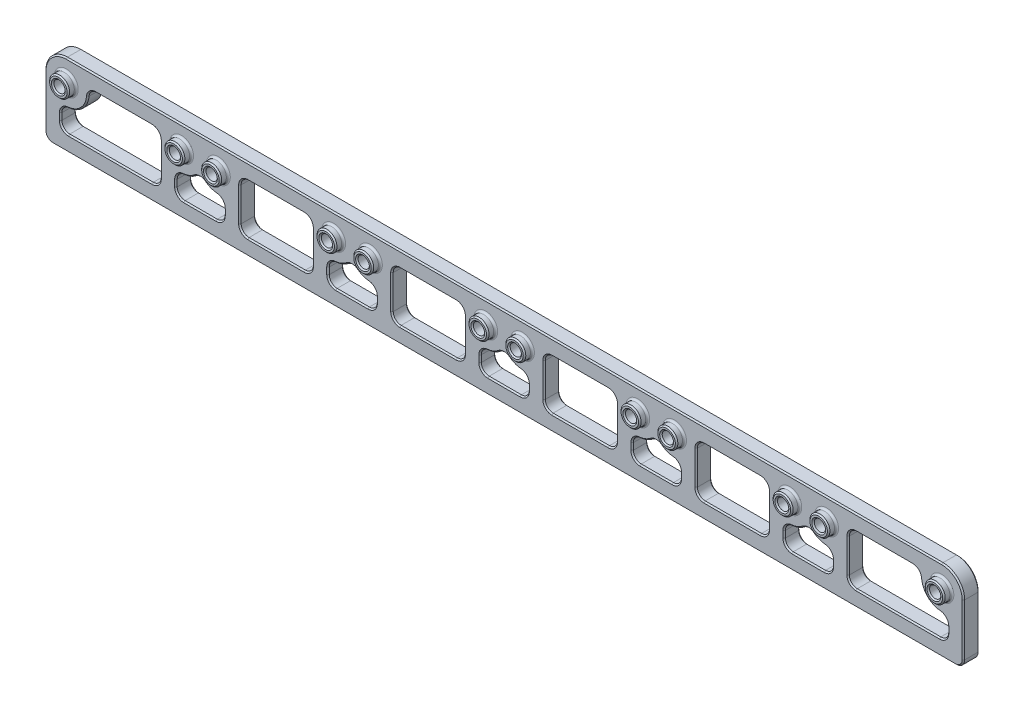
SolidWorks part; units mm, degrees
ref_plane "Front Plane" through (0, 0, 0) normal (0, 0, 1) x (1, 0, 0)
ref_plane "Top Plane" through (0, 0, 0) normal (0, 1, 0) x (1, 0, 0)
ref_plane "Right Plane" through (0, 0, 0) normal (1, 0, 0) x (0, 0, -1)
sketch "Sketch1" plane through (0, 0, 0) normal (0, 0, 1) x (1, 0, 0)
  line L0 (92.075, 4.3205) -> (92.075, -11.999)
  line L1 (92.075, -11.999) -> (-92.075, -11.999)
  line L2 (-92.075, -11.999) -> (-92.075, 4.3205)
  line L18 (92.075, 0) -> (-92.075, 0) construction
  line L19 (92.075, 4.3205) -> (-92.075, 4.3205)
  point P0 (88.5448, 5.9995)
  dimension "D1" = 4.3205
  dimension "D2" = 184.15
  dimension "D3" = 11.999
extrude "Boss-Extrude1" add sketch "Sketch1" along normal mid plane 3.175
sketch "Sketch2" plane through (0, 0, 1.5875) normal (0, 0, 1) x (1, 0, 0)
  line L0 (-3.6855, 0) -> (3.6855, 0) construction
  line L1 (-87.7545, 0) -> (-64.6455, 0) construction
  line L2 (-64.6455, 0) -> (-57.2745, 0) construction
  line L3 (-57.2745, 0) -> (-34.1655, 0) construction
  line L4 (-34.1655, 0) -> (-26.7945, 0) construction
  line L5 (-26.7945, 0) -> (-3.6855, 0) construction
  line L6 (3.6855, 0) -> (26.7945, 0) construction
  line L7 (26.7945, 0) -> (34.1655, 0) construction
  line L8 (34.1655, 0) -> (57.2745, 0) construction
  line L9 (57.2745, 0) -> (64.6455, 0) construction
  line L10 (64.6455, 0) -> (87.7545, 0) construction
  circle A0 centre (-87.7545, 0) radius 2.0002
  circle A1 centre (-64.6455, 0) radius 2.0002
  circle A2 centre (-57.2745, 0) radius 2.0003
  circle A3 centre (-34.1655, 0) radius 2.0003
  circle A4 centre (-26.7945, 0) radius 2.0003
  circle A5 centre (-3.6855, 0) radius 2.0002
  circle A6 centre (3.6855, 0) radius 2.0003
  circle A7 centre (26.7945, 0) radius 2.0002
  circle A8 centre (34.1655, 0) radius 2.0003
  circle A9 centre (57.2745, 0) radius 2.0003
  circle A10 centre (64.6455, 0) radius 2.0002
  circle A11 centre (87.7545, 0) radius 2.0002
  dimension "D1" = 4.0005
  dimension "D2" = 23.1089
  dimension "D3" = 7.3711
  dimension "D4" = 23.1089
  dimension "D5" = 7.3711
  dimension "D6" = 23.1089
  dimension "D7" = 7.3711
  dimension "D8" = 23.1089
  dimension "D9" = 7.3711
  dimension "D10" = 23.1089
  dimension "D11" = 7.3711
  dimension "D12" = 23.1089
extrude "Boss-Extrude2" add sketch "Sketch2" along normal blind 1.5875 contours A0
hole_wizard "#4-40 Tapped Hole1" positions "Sketch3" profile "Sketch4" tap size "#4-40" standard "ANSI Inch" end condition through all
sketch "Sketch3" plane through (0, 0, 3.175) normal (0, 0, 1) x (1, 0, 0)
  circle A0 centre (-87.7545, 0) radius 2.0002 construction
  point P0 (-87.7545, 0)
  point P2 (-64.6455, 0)
  point P5 (-57.2745, 0)
  point P8 (-34.1655, 0)
  point P11 (-26.7945, 0)
  point P14 (-3.6855, 0)
  point P17 (3.6855, 0)
  point P20 (26.7945, 0)
  point P23 (34.1655, 0)
  point P26 (57.2745, 0)
  point P29 (64.6455, 0)
  point P32 (87.7545, 0)
sketch "Sketch4" plane through (-87.7545, 0, 3.175) normal (1, 0, 0) x (0, -1, 0)
  line L0 (0, 0) -> (0, 4.7625)
  line L1 (0, 4.7625) -> (1.1303, 4.7625)
  line L2 (1.1303, 4.7625) -> (1.1303, 0)
  line L5 (1.1303, 0) -> (0, 0)
  line L11 (0, -6.35) -> (0, 107.95) construction
  dimension "Thru Tap Drill Dia." = 2.2606
  dimension "Thru Tap Drill Depth" = 4.7625
cosmetic thread "Hole Thread1" parameters "D2"=2.8448
cosmetic thread "Hole Thread2" parameters "D2"=2.8448
cosmetic thread "Hole Thread3" parameters "D2"=2.8448
cosmetic thread "Hole Thread4" parameters "D2"=2.8448
cosmetic thread "Hole Thread5" parameters "D2"=2.8448
cosmetic thread "Hole Thread6" parameters "D2"=2.8448
cosmetic thread "Hole Thread7" parameters "D2"=2.8448
cosmetic thread "Hole Thread8" parameters "D2"=2.8448
cosmetic thread "Hole Thread9" parameters "D2"=2.8448
cosmetic thread "Hole Thread10" parameters "D2"=2.8448
cosmetic thread "Hole Thread11" parameters "D2"=2.8448
cosmetic thread "Hole Thread12" parameters "D2"=2.8448
sketch "Sketch5" plane through (0, 0, 1.5875) normal (0, 0, 1) x (1, 0, 0)
  line L0 (92.075, 4.3205) -> (-92.075, 4.3205) construction
  line L1 (-83.5844, 1.1303) -> (-68.8156, 1.1303)
  line L2 (-53.1044, 1.1303) -> (-38.3356, 1.1303)
  line L3 (-22.6244, 1.1303) -> (-7.8556, 1.1303)
  line L4 (7.8556, 1.1303) -> (22.6244, 1.1303)
  line L5 (38.3356, 1.1303) -> (53.1044, 1.1303)
  line L6 (68.8156, 1.1303) -> (83.5844, 1.1303)
  line L7 (-88.8848, -4.1701) -> (-88.8848, -8.8087)
  line L8 (-92.075, 4.3205) -> (-92.075, -11.999) construction
  line L9 (-88.8848, -8.8087) -> (-68.9661, -8.8087)
  line L10 (-68.9661, -8.8087) -> (-68.9661, 0)
  line L11 (-92.075, -11.999) -> (92.075, -11.999) construction
  line L12 (-65.7758, -4.1701) -> (-65.7758, -8.8087)
  line L13 (-65.7758, -8.8087) -> (-56.1442, -8.8087)
  line L14 (-56.1442, -8.8087) -> (-56.1442, -4.1701)
  line L15 (-52.9539, 0) -> (-52.9539, -8.8087)
  line L16 (-52.9539, -8.8087) -> (-38.4861, -8.8087)
  line L17 (-38.4861, -8.8087) -> (-38.4861, 0)
  line L18 (-35.2958, -4.1701) -> (-35.2958, -8.8087)
  line L19 (-35.2958, -8.8087) -> (-25.6642, -8.8087)
  line L20 (-25.6642, -8.8087) -> (-25.6642, -4.1701)
  line L21 (-22.4739, 0) -> (-22.4739, -8.8087)
  line L22 (-22.4739, -8.8087) -> (-8.0061, -8.8087)
  line L23 (-8.0061, -8.8087) -> (-8.0061, 0)
  line L24 (-4.8158, -4.1701) -> (-4.8158, -8.8087)
  line L25 (-4.8158, -8.8087) -> (4.8158, -8.8087)
  line L26 (4.8158, -8.8087) -> (4.8158, -4.1701)
  line L27 (8.0061, 0) -> (8.0061, -8.8087)
  line L28 (8.0061, -8.8087) -> (22.4739, -8.8087)
  line L29 (22.4739, -8.8087) -> (22.4739, 0)
  line L30 (25.6642, -4.1701) -> (25.6642, -8.8087)
  line L31 (25.6642, -8.8087) -> (35.2958, -8.8087)
  line L32 (35.2958, -8.8087) -> (35.2958, -4.1701)
  line L33 (38.4861, 0) -> (38.4861, -8.8087)
  line L34 (38.4861, -8.8087) -> (52.9539, -8.8087)
  line L35 (52.9539, -8.8087) -> (52.9539, 0)
  line L36 (56.1442, -4.1701) -> (56.1442, -8.8087)
  line L37 (56.1442, -8.8087) -> (65.7758, -8.8087)
  line L38 (65.7758, -8.8087) -> (65.7758, -4.1701)
  line L39 (68.9661, 0) -> (68.9661, -8.8087)
  line L40 (68.9661, -8.8087) -> (88.8848, -8.8087)
  line L41 (88.8848, -4.1701) -> (88.8848, -8.8087)
  line L42 (92.075, -11.999) -> (92.075, 4.3205) construction
  line L43 (-92.075, 0) -> (-92.075, 4.3205)
  line L44 (-92.075, 4.3205) -> (-87.7545, 4.3205)
  line L45 (87.7545, 4.3205) -> (92.075, 4.3205)
  line L46 (92.075, 4.3205) -> (92.075, 0)
  arc A0 (-88.8848, -4.1701) -> (-83.5844, 1.1303) centre (-87.7545, 0) ccw
  arc A1 (-68.8156, 1.1303) -> (-68.9661, 0) centre (-64.6455, 0) ccw
  arc A2 (-60.96, -2.2547) -> (-56.1442, -4.1701) centre (-57.2745, 0) ccw
  arc A3 (-38.3356, 1.1303) -> (-38.4861, 0) centre (-34.1655, 0) ccw
  arc A4 (-30.48, -2.2547) -> (-25.6642, -4.1701) centre (-26.7945, 0) ccw
  arc A5 (-7.8556, 1.1303) -> (-8.0061, 0) centre (-3.6855, 0) ccw
  arc A6 (0, -2.2547) -> (4.8158, -4.1701) centre (3.6855, 0) ccw
  arc A7 (22.6244, 1.1303) -> (22.4739, 0) centre (26.7945, 0) ccw
  arc A8 (30.48, -2.2547) -> (35.2958, -4.1701) centre (34.1655, 0) ccw
  arc A9 (53.1044, 1.1303) -> (52.9539, 0) centre (57.2745, 0) ccw
  arc A10 (60.96, -2.2547) -> (65.7758, -4.1701) centre (64.6455, 0) ccw
  arc A11 (83.5844, 1.1303) -> (88.8848, -4.1701) centre (87.7545, 0) ccw
  arc A12 (-65.7758, -4.1701) -> (-60.96, -2.2547) centre (-64.6455, 0) ccw
  arc A13 (-52.9539, 0) -> (-53.1044, 1.1303) centre (-57.2745, 0) ccw
  arc A14 (-35.2958, -4.1701) -> (-30.48, -2.2547) centre (-34.1655, 0) ccw
  arc A15 (-22.4739, 0) -> (-22.6244, 1.1303) centre (-26.7945, 0) ccw
  arc A16 (-4.8158, -4.1701) -> (0, -2.2547) centre (-3.6855, 0) ccw
  arc A17 (8.0061, 0) -> (7.8556, 1.1303) centre (3.6855, 0) ccw
  arc A18 (25.6642, -4.1701) -> (30.48, -2.2547) centre (26.7945, 0) ccw
  arc A19 (38.4861, 0) -> (38.3356, 1.1303) centre (34.1655, 0) ccw
  arc A20 (68.9661, 0) -> (68.8156, 1.1303) centre (64.6455, 0) ccw
  arc A21 (56.1442, -4.1701) -> (60.96, -2.2547) centre (57.2745, 0) ccw
  arc A22 (-87.7545, 4.3205) -> (-92.075, 0) centre (-87.7545, 0) ccw
  arc A23 (92.075, 0) -> (87.7545, 4.3205) centre (87.7545, 0) ccw
  point P66 (-56.1442, -6.4894)
  dimension "D1" = 3.1902
  dimension "D2" = 3.1902
  dimension "D3" = 3.1902
  dimension "D4" = 3.1902
  dimension "D5" = 3.1902
  dimension "D6" = 3.1902
  dimension "D7" = 3.1902
  dimension "D8" = 3.1902
  dimension "D9" = 3.1902
  dimension "D10" = 3.1902
  dimension "D11" = 3.1902
  dimension "D12" = 3.1902
  dimension "D13" = 3.1902
  dimension "D14" = 3.1902
extrude "Cut-Extrude1" cut sketch "Sketch5" against normal through all both and the other way through all contours A4 L20 L19 L18 A14
fillet "Fillet1" radius 0.3969 12 edges at (85.7542, 0, 1.5875) (62.6453, 0, 1.5875) (55.2742, 0, 1.5875) (32.1653, 0, 1.5875) (24.7942, 0, 1.5875) (1.6853, 0, 1.5875) (-5.6858, 0, 1.5875) (-28.7947, 0, 1.5875) (-36.1658, 0, 1.5875) (-59.2747, 0, 1.5875) (-66.6458, 0, 1.5875) (-89.7547, 0, 1.5875)
fillet "Fillet2" radius 1.5875 53 edges at (-92.075, -11.999, 0) (92.075, -11.999, 0) (83.5844, 1.1303, 0) (88.8848, -4.1701, 0) (88.8848, -8.8087, 0) (68.9661, -8.8087, 0) (68.8156, 1.1303, 0) (65.7758, -4.1701, 0) (65.7758, -8.8087, 0) (56.1442, -8.8087, 0) (56.1442, -4.1701, 0) (60.96, -2.2547, 0) (53.1044, 1.1303, 0) (52.9539, -8.8087, 0) (38.4861, -8.8087, 0) (38.3356, 1.1303, 0) (25.6642, -4.1701, 0) (30.48, -2.2547, 0) (35.2958, -4.1701, 0) (35.2958, -8.8087, 0) (25.6642, -8.8087, 0) (8.0061, -8.8087, 0) (22.4739, -8.8087, 0) (22.6244, 1.1303, 0) (7.8556, 1.1303, 0) (-4.8158, -4.1701, 0) (4.8158, -4.1701, 0) (0, -2.2547, 0) (-4.8158, -8.8087, 0) (4.8158, -8.8087, 0) (-8.0061, -8.8087, 0) (-7.8556, 1.1303, 0) (-22.6244, 1.1303, 0) (-22.4739, -8.8087, 0) (-25.6642, -8.8087, 0) (-25.6642, -4.1701, 0) (-30.48, -2.2547, 0) (-35.2958, -4.1701, 0) (-35.2958, -8.8087, 0) (-38.4861, -8.8087, 0) (-38.3356, 1.1303, 0) (-53.1044, 1.1303, 0) (-52.9539, -8.8087, 0) (-56.1442, -8.8087, 0) (-65.7758, -8.8087, 0) (-65.7758, -4.1701, 0) (-56.1442, -4.1701, 0) (-88.8848, -4.1701, 0) (-88.8848, -8.8087, 0) (-68.9661, -8.8087, 0) (-68.8156, 1.1303, 0) (-83.5844, 1.1303, 0) (-60.96, -2.2547, 0)
chamfer "Chamfer2" distance 0.254 angle 45 256 edges at (89.7547, 0, 3.175) (66.6458, 0, 3.175) (59.2747, 0, 3.175) (36.1658, 0, 3.175) (28.7947, 0, 3.175) (5.6858, 0, 3.175) (-1.6853, 0, 3.175) (-24.7942, 0, 3.175) (-32.1653, 0, 3.175) (-55.2742, 0, 3.175) (-62.6453, 0, 3.175) (-85.7542, 0, 3.175) (88.8848, 0, 3.175) (88.8848, 0, -1.5875) (65.7758, 0, 3.175) (65.7758, 0, -1.5875) (58.4048, 0, 3.175) (58.4048, 0, -1.5875) (35.2958, 0, 3.175) (35.2958, 0, -1.5875) (27.9248, 0, 3.175) (27.9248, 0, -1.5875) (4.8158, 0, 3.175) (4.8158, 0, -1.5875) (-2.5552, 0, 3.175) (-2.5552, 0, -1.5875) (-25.6642, 0, 3.175) (-25.6642, 0, -1.5875) (-33.0352, 0, 3.175) (-33.0352, 0, -1.5875) (-56.1442, 0, 3.175) (-56.1442, 0, -1.5875) (-63.5152, 0, 3.175) (-63.5152, 0, -1.5875) (-86.6242, 0, 3.175) (-86.6242, 0, -1.5875) (82.9424, 0.708, -1.5875) (84.6994, -3.0551, -1.5875) (88.4624, -4.8121, -1.5875) (88.8848, -6.5558, -1.5875) (88.4198, -8.3438, -1.5875) (78.9254, -8.8087, -1.5875) (69.431, -8.3438, -1.5875) (68.9661, -3.8392, -1.5875) (69.431, 0.6653, -1.5875) (76.2089, 1.1303, -1.5875) (52.489, 0.6653, -1.5875) (52.9539, -3.8392, -1.5875) (52.489, -8.3438, -1.5875) (45.72, -8.8087, -1.5875) (38.951, -8.3438, -1.5875) (38.4861, -3.8392, -1.5875) (38.951, 0.6653, -1.5875) (45.72, 1.1303, -1.5875) (22.009, 0.6653, -1.5875) (22.4739, -3.8392, -1.5875) (22.009, -8.3438, -1.5875) (15.24, -8.8087, -1.5875) (8.471, -8.3438, -1.5875) (8.0061, -3.8392, -1.5875) (8.471, 0.6653, -1.5875) (15.24, 1.1303, -1.5875) (-8.471, 0.6653, -1.5875) (-8.0061, -3.8392, -1.5875) (-8.471, -8.3438, -1.5875) (-15.24, -8.8087, -1.5875) (-22.009, -8.3438, -1.5875) (-22.4739, -3.8392, -1.5875) (-22.009, 0.6653, -1.5875) (-15.24, 1.1303, -1.5875) (-56.5665, -4.8121, -1.5875) (-56.1442, -6.5558, -1.5875) (-56.6091, -8.3438, -1.5875) (-60.96, -8.8087, -1.5875) (-65.3109, -8.3438, -1.5875) (-65.7758, -6.5558, -1.5875) (-65.3535, -4.8121, -1.5875) (-63.0609, -4.0194, -1.5875) (-60.96, -3.03, -1.5875) (-58.8591, -4.0194, -1.5875) (-26.0865, -4.8121, -1.5875) (-25.6642, -6.5558, -1.5875) (-26.1291, -8.3438, -1.5875) (-30.48, -8.8087, -1.5875) (-34.8309, -8.3438, -1.5875) (-35.2958, -6.5558, -1.5875) (-34.8735, -4.8121, -1.5875) (-32.5809, -4.0194, -1.5875) (-30.48, -3.03, -1.5875) (-28.3791, -4.0194, -1.5875) (4.3935, -4.8121, -1.5875) (4.8158, -6.5558, -1.5875) (4.3509, -8.3438, -1.5875) (0, -8.8087, -1.5875) (-4.3509, -8.3438, -1.5875) (-4.8158, -6.5558, -1.5875) (-4.3935, -4.8121, -1.5875) (-2.1009, -4.0194, -1.5875) (0, -3.03, -1.5875) (2.1009, -4.0194, -1.5875) (34.8735, -4.8121, -1.5875) (35.2958, -6.5558, -1.5875) (34.8309, -8.3438, -1.5875) (30.48, -8.8087, -1.5875) (26.1291, -8.3438, -1.5875) (25.6642, -6.5558, -1.5875) (26.0865, -4.8121, -1.5875) (28.3791, -4.0194, -1.5875) (30.48, -3.03, -1.5875) (32.5809, -4.0194, -1.5875) (65.3535, -4.8121, -1.5875) (65.7758, -6.5558, -1.5875) (65.3109, -8.3438, -1.5875) (60.96, -8.8087, -1.5875) (56.6091, -8.3438, -1.5875) (56.1442, -6.5558, -1.5875) (56.5665, -4.8121, -1.5875) (58.8591, -4.0194, -1.5875) (60.96, -3.03, -1.5875) (63.0609, -4.0194, -1.5875) (91.61, -11.534, -1.5875) (92.075, -5.2057, -1.5875) (90.8095, 3.0551, -1.5875) (0, 4.3205, -1.5875) (-90.8095, 3.0551, -1.5875) (-92.075, -5.2057, -1.5875) (-91.61, -11.534, -1.5875) (0, -11.999, -1.5875) (-69.431, 0.6653, -1.5875) (-68.9661, -3.8392, -1.5875) (-69.431, -8.3438, -1.5875) (-78.9254, -8.8087, -1.5875) (-88.4198, -8.3438, -1.5875) (-88.8848, -6.5558, -1.5875) (-88.4624, -4.8121, -1.5875) (-84.6994, -3.0551, -1.5875) (-82.9424, 0.708, -1.5875) (-76.2089, 1.1303, -1.5875) (-38.951, 0.6653, -1.5875) (-38.4861, -3.8392, -1.5875) (-38.951, -8.3438, -1.5875) (-45.72, -8.8087, -1.5875) (-52.489, -8.3438, -1.5875) (-52.9539, -3.8392, -1.5875) (-52.489, 0.6653, -1.5875) (-45.72, 1.1303, -1.5875) (-90.8095, 3.0551, 1.5875) (0, 4.3205, 1.5875) (90.8095, 3.0551, 1.5875) (92.075, -5.2057, 1.5875) (91.61, -11.534, 1.5875) (0, -11.999, 1.5875) (-91.61, -11.534, 1.5875) (-92.075, -5.2057, 1.5875) (88.4198, -8.3438, 1.5875) (88.8848, -6.5558, 1.5875) (88.4624, -4.8121, 1.5875) (84.6994, -3.0551, 1.5875) (82.9424, 0.708, 1.5875) (76.2089, 1.1303, 1.5875) (69.431, 0.6653, 1.5875) (68.9661, -3.8392, 1.5875) (69.431, -8.3438, 1.5875) (78.9254, -8.8087, 1.5875) (52.489, -8.3438, 1.5875) (52.9539, -3.8392, 1.5875) (52.489, 0.6653, 1.5875) (45.72, 1.1303, 1.5875) (38.951, 0.6653, 1.5875) (38.4861, -3.8392, 1.5875) (38.951, -8.3438, 1.5875) (45.72, -8.8087, 1.5875) (22.009, -8.3438, 1.5875) (22.4739, -3.8392, 1.5875) (22.009, 0.6653, 1.5875) (15.24, 1.1303, 1.5875) (8.471, 0.6653, 1.5875) (8.0061, -3.8392, 1.5875) (8.471, -8.3438, 1.5875) (15.24, -8.8087, 1.5875) (-8.471, -8.3438, 1.5875) (-8.0061, -3.8392, 1.5875) (-8.471, 0.6653, 1.5875) (-15.24, 1.1303, 1.5875) (-22.009, 0.6653, 1.5875) (-22.4739, -3.8392, 1.5875) (-22.009, -8.3438, 1.5875) (-15.24, -8.8087, 1.5875) (-56.6091, -8.3438, 1.5875) (-56.1442, -6.5558, 1.5875) (-56.5665, -4.8121, 1.5875) (-58.8591, -4.0194, 1.5875) (-60.96, -3.03, 1.5875) (-63.0609, -4.0194, 1.5875) (-65.3535, -4.8121, 1.5875) (-65.7758, -6.5558, 1.5875) (-65.3109, -8.3438, 1.5875) (-60.96, -8.8087, 1.5875) (-26.1291, -8.3438, 1.5875) (-25.6642, -6.5558, 1.5875) (-26.0865, -4.8121, 1.5875) (-28.3791, -4.0194, 1.5875) (-30.48, -3.03, 1.5875) (-32.5809, -4.0194, 1.5875) (-34.8735, -4.8121, 1.5875) (-35.2958, -6.5558, 1.5875) (-34.8309, -8.3438, 1.5875) (-30.48, -8.8087, 1.5875) (4.3509, -8.3438, 1.5875) (4.8158, -6.5558, 1.5875) (4.3935, -4.8121, 1.5875) (2.1009, -4.0194, 1.5875) (0, -3.03, 1.5875) (-2.1009, -4.0194, 1.5875) (-4.3935, -4.8121, 1.5875) (-4.8158, -6.5558, 1.5875) (-4.3509, -8.3438, 1.5875) (0, -8.8087, 1.5875) (34.8309, -8.3438, 1.5875) (35.2958, -6.5558, 1.5875) (34.8735, -4.8121, 1.5875) (32.5809, -4.0194, 1.5875) (30.48, -3.03, 1.5875) (28.3791, -4.0194, 1.5875) (26.0865, -4.8121, 1.5875) (25.6642, -6.5558, 1.5875) (26.1291, -8.3438, 1.5875) (30.48, -8.8087, 1.5875) (65.3109, -8.3438, 1.5875) (65.7758, -6.5558, 1.5875) (65.3535, -4.8121, 1.5875) (63.0609, -4.0194, 1.5875) (60.96, -3.03, 1.5875) (58.8591, -4.0194, 1.5875) (56.5665, -4.8121, 1.5875) (56.1442, -6.5558, 1.5875) (56.6091, -8.3438, 1.5875) (60.96, -8.8087, 1.5875) (-69.431, -8.3438, 1.5875) (-68.9661, -3.8392, 1.5875) (-69.431, 0.6653, 1.5875) (-76.2089, 1.1303, 1.5875) (-82.9424, 0.708, 1.5875) (-84.6994, -3.0551, 1.5875) (-88.4624, -4.8121, 1.5875) (-88.8848, -6.5558, 1.5875) (-88.4198, -8.3438, 1.5875) (-78.9254, -8.8087, 1.5875) (-38.951, -8.3438, 1.5875) (-38.4861, -3.8392, 1.5875) (-38.951, 0.6653, 1.5875) (-45.72, 1.1303, 1.5875) (-52.489, 0.6653, 1.5875) (-52.9539, -3.8392, 1.5875) (-52.489, -8.3438, 1.5875) (-45.72, -8.8087, 1.5875)
equation "\"D2@Sketch5\"=\"D1@Sketch5\""
equation "\"D3@Sketch5\"=\"D1@Sketch5\""
equation "\"D4@Sketch5\"=\"D1@Sketch5\""
equation "\"D5@Sketch5\"=\"D1@Sketch5\""
equation "\"D6@Sketch5\"=\"D1@Sketch5\""
equation "\"D7@Sketch5\"=\"D1@Sketch5\""
equation "\"D8@Sketch5\"=\"D1@Sketch5\""
equation "\"D9@Sketch5\"=\"D1@Sketch5\""
equation "\"D10@Sketch5\"=\"D1@Sketch5\""
equation "\"D11@Sketch5\"=\"D1@Sketch5\""
equation "\"D12@Sketch5\"=\"D1@Sketch5\""
equation "\"D13@Sketch5\"=\"D1@Sketch5\""
equation "\"D14@Sketch5\"=\"D1@Sketch5\""
